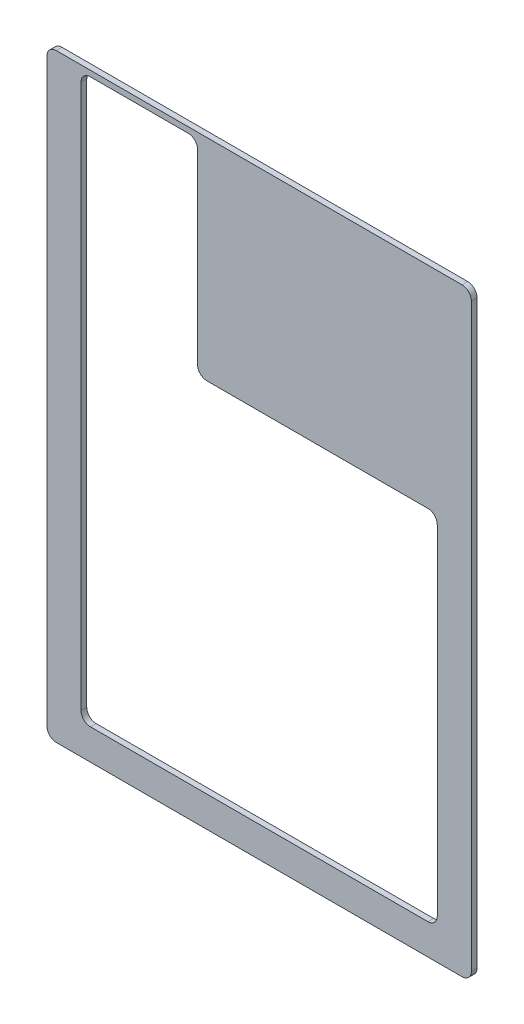
SolidWorks part; units mm, degrees
ref_plane "Front Plane" through (0, 0, 0) normal (0, 0, 1) x (1, 0, 0)
ref_plane "Top Plane" through (0, 0, 0) normal (0, 1, 0) x (1, 0, 0)
ref_plane "Right Plane" through (0, 0, 0) normal (1, 0, 0) x (0, 0, -1)
sketch "Sketch1" plane through (0, 0, 0) normal (0, 0, 1) x (1, 0, 0)
  line L1 (-161.925, -228.6) -> (161.925, -228.6)
  line L2 (-161.925, -228.6) -> (-161.925, 228.6)
  line L3 (-161.925, 228.6) -> (161.925, 228.6)
  line L4 (161.925, -228.6) -> (161.925, 228.6)
  line L5 (-161.925, -228.6) -> (161.925, 228.6) construction
  line L6 (-161.925, 228.6) -> (161.925, -228.6) construction
  point P0 (0, 0)
  dimension "D1" = 323.85
  dimension "D2" = 457.2
extrude "Boss-Extrude1" add sketch "Sketch1" along normal blind 4.3434
sketch "Sketch2" plane through (0, 0, 4.3434) normal (0, 0, 1) x (1, 0, 0)
  line L0 (0, 228.6) -> (0, -228.6) construction
  line L1 (-135.89, -205.232) -> (135.89, -205.232)
  line L2 (-135.89, -205.232) -> (-135.89, 67.818)
  line L3 (-135.89, 67.818) -> (135.89, 67.818)
  line L4 (135.89, -205.232) -> (135.89, 67.818)
  line L5 (-135.89, -205.232) -> (135.89, 67.818) construction
  line L6 (-135.89, 67.818) -> (135.89, -205.232) construction
  line L7 (161.925, 228.6) -> (-161.925, 228.6) construction
  line L8 (-161.925, -228.6) -> (161.925, -228.6) construction
  point P0 (0, -65.2276)
  point P12 (0, -68.707)
  dimension "D1" = 271.78
  dimension "D2" = 273.05
  dimension "D3" = 23.368
extrude "Cut-Extrude1" cut sketch "Sketch2" against normal through all
fillet "Fillet1" radius 7.1437 8 edges at (135.89, -205.232, 2.1717) (135.89, 67.818, 2.1717) (-135.89, 67.818, 2.1717) (-135.89, -205.232, 2.1717) (-161.925, -228.6, 2.1717) (161.925, -228.6, 2.1717) (161.925, 228.6, 2.1717) (-161.925, 228.6, 2.1717)
sketch "Sketch4" plane through (0, 0, 4.3434) normal (0, 0, 1) x (1, 0, 0)
  line L0 (-135.89, 39.3453) -> (-135.89, 224.2566)
  line L1 (-135.89, 39.3453) -> (-46.99, 39.3453)
  line L2 (-135.89, 224.2566) -> (-46.99, 224.2566)
  line L3 (-46.99, 39.3453) -> (-46.99, 224.2566)
  line L4 (-135.89, 60.6743) -> (-135.89, -198.0883) construction
  line L6 (154.7812, 228.6) -> (-154.7813, 228.6) construction
  dimension "D1" = 88.9
  dimension "D2" = 4.3434
extrude "Cut-Extrude3" cut sketch "Sketch4" against normal through all
fillet "Fillet2" radius 7.1437 3 edges at (-46.99, 67.818, 2.1717) (-46.99, 224.2566, 2.1717) (-135.89, 224.2566, 2.1717)
